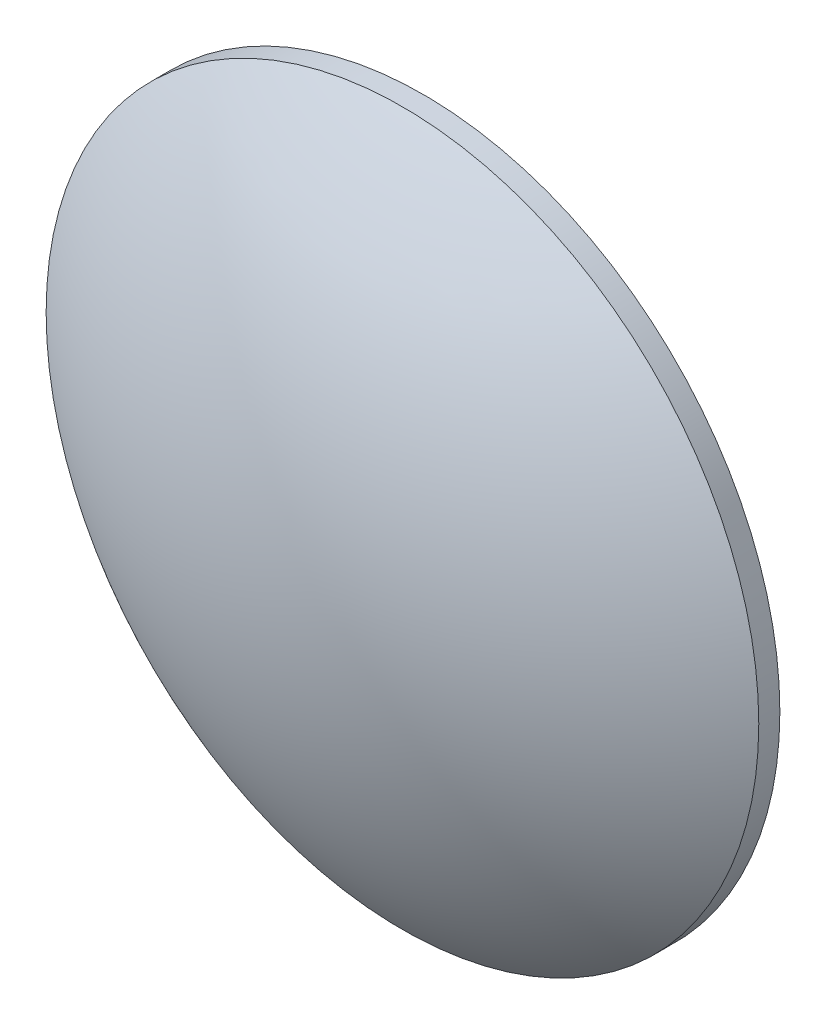
SolidWorks part; units mm, degrees
ref_plane "Front Plane" through (0, 0, 0) normal (0, 0, 1) x (1, 0, 0)
ref_plane "Top Plane" through (0, 0, 0) normal (0, 1, 0) x (1, 0, 0)
ref_plane "Right Plane" through (0, 0, 0) normal (1, 0, 0) x (0, 0, -1)
sketch "Sketch1" plane through (0, 0, 0) normal (0, 0, 1) x (1, 0, 0)
  line L0 (0, 42.738) -> (0, -42.738) construction
  line L1 (0, -47.0118) -> (0, 47.0118) construction
  line L2 (0, 42.738) -> (0, -42.738)
  arc A0 (0, 42.738) -> (0, -42.738) centre (0, 0) ccw
  dimension "D1" = 85.476
revolve "Revolve1" add sketch "Sketch1" angle 360 about L0
ref_plane "Plane1" through (0, 0, 42.738) normal (0, 0, 1) x (1, 0, 0)
sketch "Sketch2" plane through (0, 0, 42.738) normal (0, 0, 1) x (1, 0, 0)
  circle A0 centre (0, 0) radius 25.4
  dimension "D1" = 50.8
extrude "Cut-Extrude1" cut sketch "Sketch2" against normal through all flip side to cut
ref_plane "Plane2" through (0, 0, 32.868) normal (0, 0, 1) x (1, 0, 0)
sketch "Sketch3" plane through (0, 0, 32.868) normal (0, 0, 1) x (1, 0, 0)
  circle A0 centre (0, 0) radius 25.4
extrude "Cut-Extrude2" cut sketch "Sketch3" against normal through all
